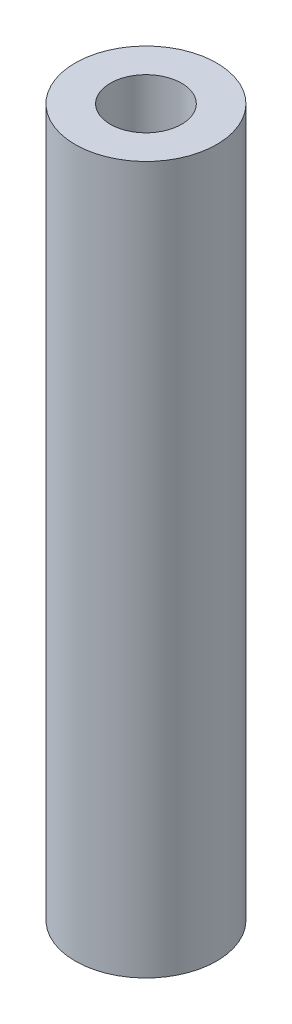
SolidWorks part; units mm, degrees
material "PP Homopolymer"
ref_plane "Front Plane" through (0, 0, 0) normal (0, 0, 1) x (1, 0, 0)
ref_plane "Top Plane" through (0, 0, 0) normal (0, 1, 0) x (1, 0, 0)
ref_plane "Right Plane" through (0, 0, 0) normal (1, 0, 0) x (0, 0, -1)
sketch "Sketch1" plane through (0, 0, 0) normal (0, 1, 0) x (1, 0, 0)
  circle A0 centre (0, 0) radius 6.35
  circle A1 centre (0, 0) radius 3.2004
  dimension "D1" = 6.4008
  dimension "D2" = 12.7
extrude "Boss-Extrude1" add sketch "Sketch1" along normal blind 63.5
